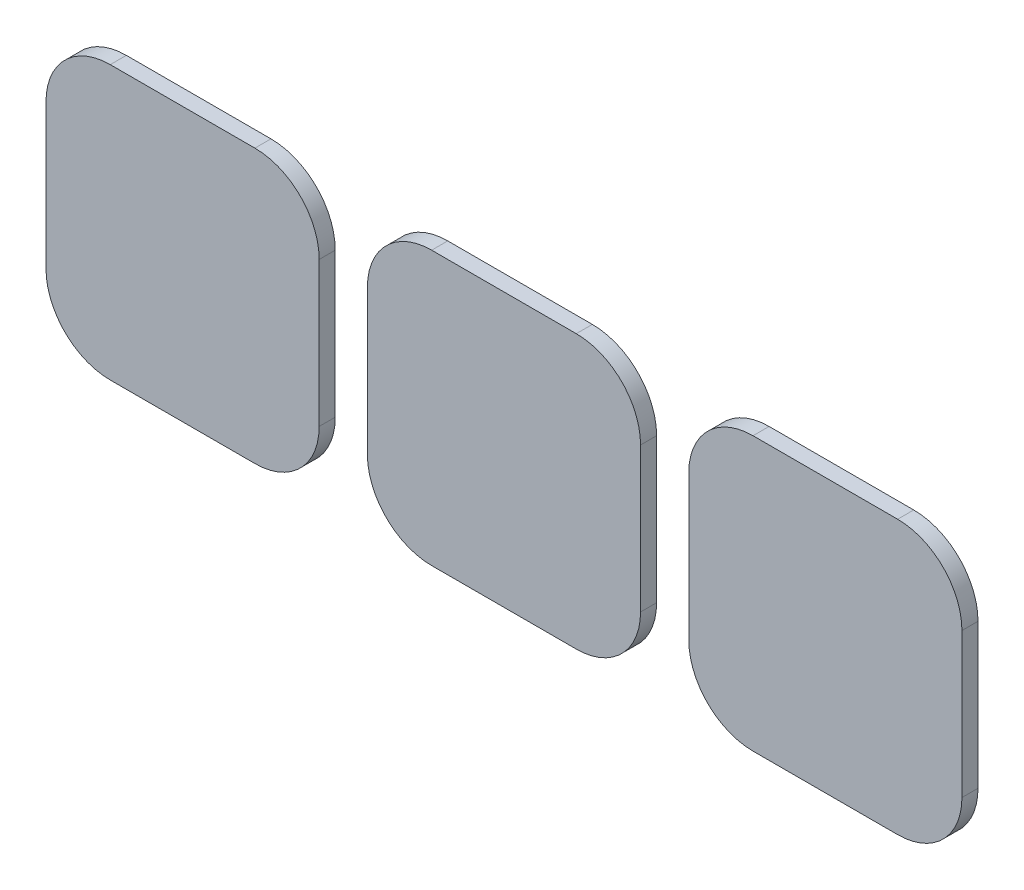
SolidWorks part; units mm, degrees
ref_plane "Front Plane" through (0, 0, 0) normal (0, 0, 1) x (1, 0, 0)
ref_plane "Top Plane" through (0, 0, 0) normal (0, 1, 0) x (1, 0, 0)
ref_plane "Right Plane" through (0, 0, 0) normal (1, 0, 0) x (0, 0, -1)
sketch "Skica1" plane through (0, 0, 0) normal (0, 0, 1) x (1, 0, 0)
  line L1 (-3.5, 2.75) -> (3.5, 2.75)
  line L2 (-3.5, 2.75) -> (-3.5, -2.75)
  line L3 (-3.5, -2.75) -> (3.5, -2.75)
  line L4 (3.5, 2.75) -> (3.5, -2.75)
  line L5 (-3.5, 2.75) -> (3.5, -2.75) construction
  line L6 (-3.5, -2.75) -> (3.5, 2.75) construction
  line L7 (-0.7, 2.25) -> (0.7, 2.25)
  line L8 (-0.7, 2.25) -> (-0.7, -2.25)
  line L9 (-0.7, -2.25) -> (0.7, -2.25)
  line L10 (0.7, 2.25) -> (0.7, -2.25)
  line L11 (-0.7, 2.25) -> (0.7, -2.25) construction
  line L12 (-0.7, -2.25) -> (0.7, 2.25) construction
  line L13 (-2.25, 0.7) -> (2.25, 0.7)
  line L14 (-2.25, 0.7) -> (-2.25, -0.7)
  line L15 (-2.25, -0.7) -> (2.25, -0.7)
  line L16 (2.25, 0.7) -> (2.25, -0.7)
  line L17 (-2.25, 0.7) -> (2.25, -0.7) construction
  line L18 (-2.25, -0.7) -> (2.25, 0.7) construction
  point P0 (0, 0)
  point P6 (0, 0)
  point P11 (0, 0)
  dimension "D1" = 1.4
  dimension "D2" = 1.4
  dimension "D3" = 4.5
  dimension "D4" = 4.5
  dimension "D5" = 5.5
  dimension "D6" = 7
extrude "Přidat vysunutím1" add sketch "Skica1" along normal blind 3.6 contours L4 L1 L2 L3 L13 L16 L15 L10 L9 L8 L14 L7
sketch "Skica2" plane through (0, 0, 3.6) normal (0, 0, 1) x (1, 0, 0)
  line L1 (-8.5, 8.5) -> (8.5, 8.5)
  line L2 (-8.5, 8.5) -> (-8.5, -8.5)
  line L3 (-8.5, -8.5) -> (8.5, -8.5)
  line L4 (8.5, 8.5) -> (8.5, -8.5)
  line L5 (-8.5, 8.5) -> (8.5, -8.5) construction
  line L6 (-8.5, -8.5) -> (8.5, 8.5) construction
  point P0 (0, 0)
  dimension "D1" = 17
  dimension "D2" = 17
extrude "Přidat vysunutím2" add sketch "Skica2" along normal blind 1
fillet "Zaoblit1" radius 4 4 edges at (-8.5, -8.5, 4.1) (8.5, -8.5, 4.1) (8.5, 8.5, 4.1) (-8.5, 8.5, 4.1)
sketch "Skica3" plane through (0, 0, 0) normal (0, 0, 1) x (1, 0, 0)
  line L0 (0, 0) -> (13.6936, 0) construction
pattern_linear "LinPole1" count 3 spacing 20 along (-1, 0, 0) of bodies 102
sketch "Skica4" plane through (0, 0, 0) normal (0, 0, -1) x (-1, 0, 0)
  line L24 (19.25, 2.3) -> (19.25, 0.75)
  line L25 (19.25, 0.75) -> (17.7, 0.75)
  line L26 (17.7, 0.75) -> (17.7, -0.75)
  line L27 (17.7, -0.75) -> (19.25, -0.75)
  line L28 (19.25, -0.75) -> (19.25, -2.3)
  line L29 (19.25, -2.3) -> (20.75, -2.3)
  line L30 (20.75, -2.3) -> (20.75, -0.75)
  line L31 (20.75, -0.75) -> (22.3, -0.75)
  line L32 (22.3, -0.75) -> (22.3, 0.75)
  line L33 (22.3, 0.75) -> (20.75, 0.75)
  line L34 (20.75, 0.75) -> (20.75, 2.3)
  line L35 (20.75, 2.3) -> (19.25, 2.3)
  line L36 (19.25, 2.3) -> (19.25, 0.75)
  line L37 (19.25, 0.75) -> (17.7, 0.75)
  line L38 (17.7, 0.75) -> (17.7, -0.75)
  line L39 (17.7, -0.75) -> (19.25, -0.75)
  line L40 (19.25, -0.75) -> (19.25, -2.3)
  line L41 (19.25, -2.3) -> (20.75, -2.3)
  line L42 (20.75, -2.3) -> (20.75, -0.75)
  line L43 (20.75, -0.75) -> (22.3, -0.75)
  line L44 (22.3, -0.75) -> (22.3, 0.75)
  line L45 (22.3, 0.75) -> (20.75, 0.75)
  line L46 (20.75, 0.75) -> (20.75, 2.3)
  line L47 (20.75, 2.3) -> (19.25, 2.3)
  line L60 (39.2, 2.35) -> (39.2, 0.8)
  line L61 (39.2, 0.8) -> (37.65, 0.8)
  line L62 (37.65, 0.8) -> (37.65, -0.8)
  line L63 (37.65, -0.8) -> (39.2, -0.8)
  line L64 (39.2, -0.8) -> (39.2, -2.35)
  line L65 (39.2, -2.35) -> (40.8, -2.35)
  line L66 (40.8, -2.35) -> (40.8, -0.8)
  line L67 (40.8, -0.8) -> (42.35, -0.8)
  line L68 (42.35, -0.8) -> (42.35, 0.8)
  line L69 (42.35, 0.8) -> (40.8, 0.8)
  line L70 (40.8, 0.8) -> (40.8, 2.35)
  line L71 (40.8, 2.35) -> (39.2, 2.35)
  line L72 (39.2, 2.35) -> (39.2, 0.8)
  line L73 (39.2, 0.8) -> (37.65, 0.8)
  line L74 (37.65, 0.8) -> (37.65, -0.8)
  line L75 (37.65, -0.8) -> (39.2, -0.8)
  line L76 (39.2, -0.8) -> (39.2, -2.35)
  line L77 (39.2, -2.35) -> (40.8, -2.35)
  line L78 (40.8, -2.35) -> (40.8, -0.8)
  line L79 (40.8, -0.8) -> (42.35, -0.8)
  line L80 (42.35, -0.8) -> (42.35, 0.8)
  line L81 (42.35, 0.8) -> (40.8, 0.8)
  line L82 (40.8, 0.8) -> (40.8, 2.35)
  line L83 (40.8, 2.35) -> (39.2, 2.35)
  dimension "D1" = 0.05
  dimension "D2" = 0.1
extrude "Odebrat vysunutím1" cut sketch "Skica4" against normal up to surface (3.6 mm away) up to face at (-20, 0, 3.6)
